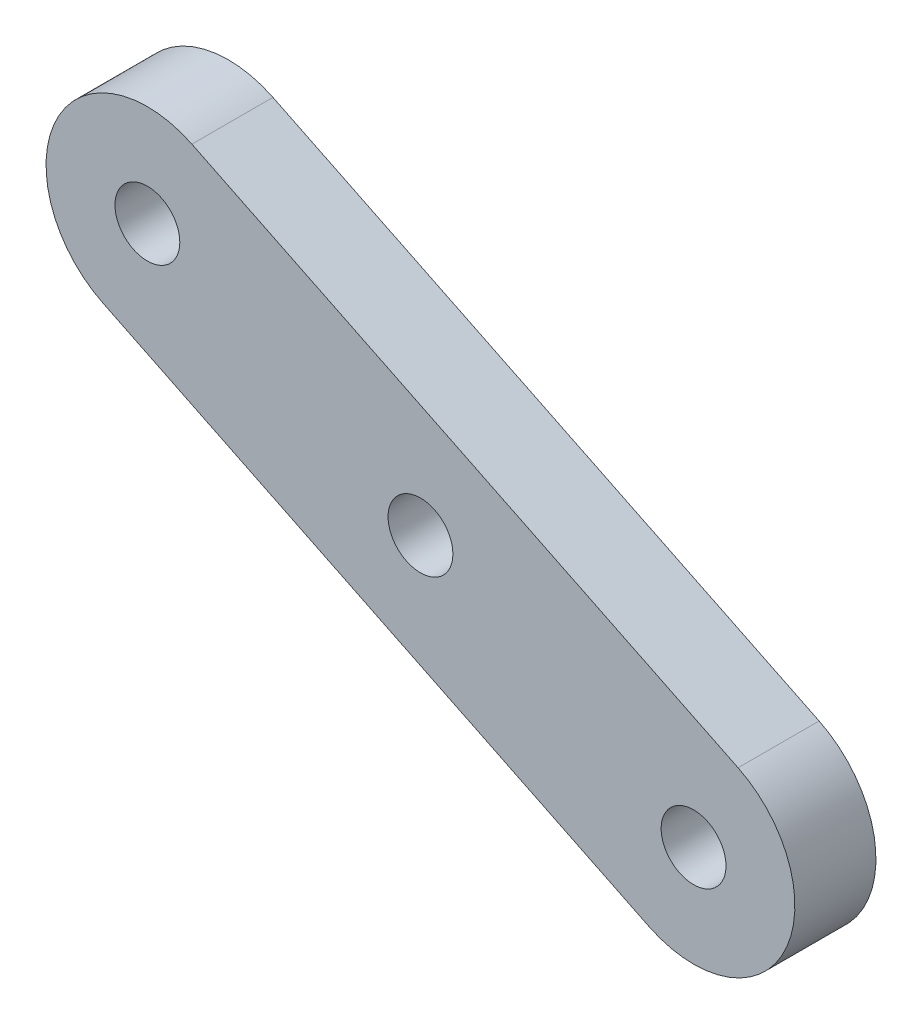
SolidWorks part; units mm, degrees
ref_plane "Front Plane" through (0, 0, 0) normal (0, 0, 1) x (1, 0, 0)
ref_plane "Top Plane" through (0, 0, 0) normal (0, 1, 0) x (1, 0, 0)
ref_plane "Right Plane" through (0, 0, 0) normal (1, 0, 0) x (0, 0, -1)
sketch "Sketch1" plane through (0, 0, 0) normal (0, 0, 1) x (1, 0, 0)
  line L0 (0, 0) -> (-26.9526, 13.1741) construction
  line L1 (-2.1957, -4.4921) -> (-29.1483, 8.682)
  line L2 (2.1957, 4.4921) -> (-24.7569, 17.6662)
  arc A0 (-2.1957, -4.4921) -> (2.1957, 4.4921) centre (0, 0) ccw
  arc A1 (-24.7569, 17.6662) -> (-29.1483, 8.682) centre (-26.9526, 13.1741) ccw
  circle A2 centre (-26.9526, 13.1741) radius 1.6
  circle A3 centre (0, 0) radius 1.6
  circle A4 centre (-13.4763, 6.5871) radius 1.6
  point P3 (-13.4763, 6.5871)
  dimension "D3" = 3.2
  dimension "D1" = 10
  dimension "D2" = 30
extrude "Boss-Extrude1" add sketch "Sketch1" along normal blind 4
